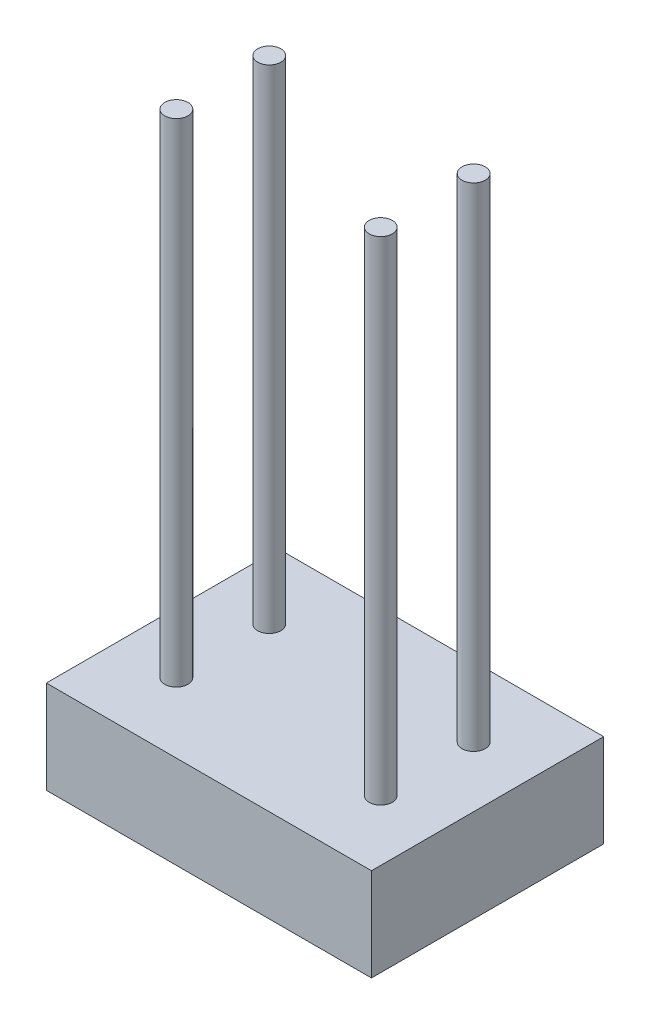
SolidWorks part; units mm, degrees
ref_plane "Front Plane" through (0, 0, 0) normal (0, 0, 1) x (1, 0, 0)
ref_plane "Top Plane" through (0, 0, 0) normal (0, 1, 0) x (1, 0, 0)
ref_plane "Right Plane" through (0, 0, 0) normal (1, 0, 0) x (0, 0, -1)
sketch "Sketch1" plane through (0, 0, 0) normal (0, 1, 0) x (1, 0, 0)
  line L1 (-175, 125) -> (175, 125)
  line L2 (-175, 125) -> (-175, -125)
  line L3 (-175, -125) -> (175, -125)
  line L4 (175, 125) -> (175, -125)
  line L5 (-175, 125) -> (175, -125) construction
  line L6 (-175, -125) -> (175, 125) construction
  point P0 (0, 0)
  dimension "D1" = 350
  dimension "D2" = 250
extrude "Boss-Extrude1" add sketch "Sketch1" along normal blind 100
sketch "Sketch3" plane through (0, 100, 0) normal (0, 1, 0) x (1, 0, 0)
  line L0 (-175, 125) -> (-175, -125) construction
  line L1 (175, 125) -> (-175, 125) construction
  line L2 (-175, 0) -> (175, 0) construction
  line L3 (175, -125) -> (175, 125) construction
  line L4 (0, 125) -> (0, -125) construction
  line L5 (-175, -125) -> (175, -125) construction
  line L7 (-110, 50) -> (110, 50) construction
  line L8 (-110, 50) -> (-110, -50) construction
  line L9 (-110, -50) -> (110, -50) construction
  line L10 (110, 50) -> (110, -50) construction
  line L11 (-110, 50) -> (110, -50) construction
  line L12 (-110, -50) -> (110, 50) construction
  circle A0 centre (-110, 50) radius 12.5
  circle A1 centre (110, 50) radius 12.5
  circle A2 centre (110, -50) radius 12.5
  circle A3 centre (-110, -50) radius 12.5
  point P20 (0, 0)
  dimension "D3" = 25
  dimension "D1" = 220
  dimension "D2" = 100
extrude "Boss-Extrude2" add sketch "Sketch3" along normal blind 530
